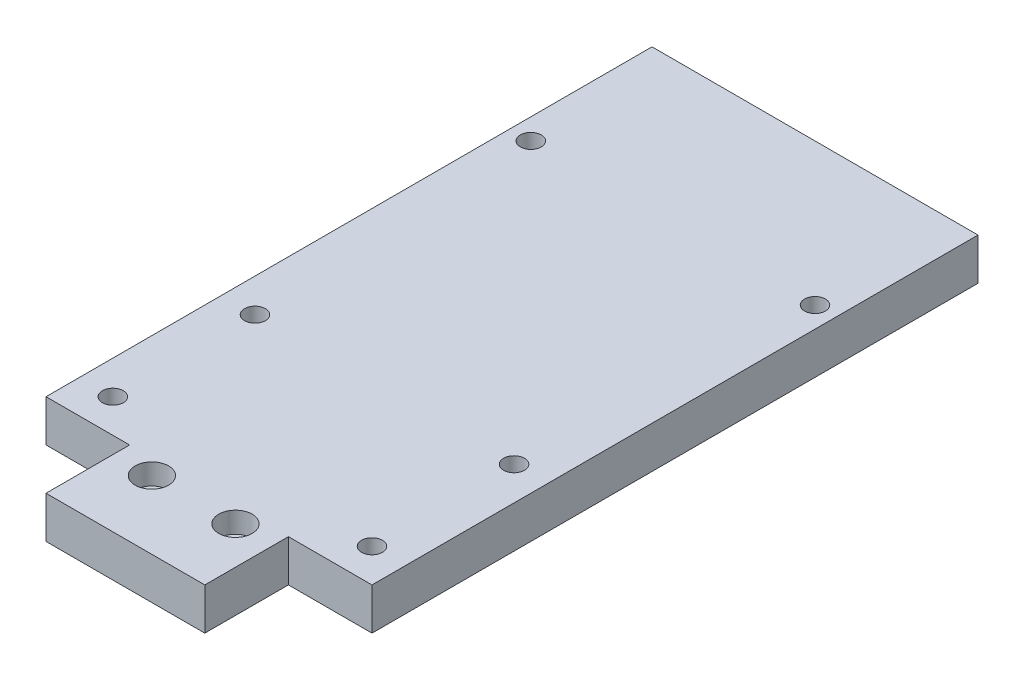
SolidWorks part; units mm, degrees
ref_plane "Front Plane" through (0, 0, 0) normal (0, 0, 1) x (1, 0, 0)
ref_plane "Top Plane" through (0, 0, 0) normal (0, 1, 0) x (1, 0, 0)
ref_plane "Right Plane" through (0, 0, 0) normal (1, 0, 0) x (0, 0, -1)
sketch "Sketch1" plane through (0, 0, 0) normal (0, 1, 0) x (1, 0, 0)
  line L0 (0, 0) -> (38, 0)
  line L1 (38, 0) -> (38, 20)
  line L2 (38, 20) -> (58, 20)
  line L3 (58, 20) -> (58, 165)
  line L4 (58, 165) -> (-20, 165)
  line L5 (-20, 165) -> (-20, 20)
  line L6 (-20, 20) -> (0, 20)
  line L7 (0, 20) -> (0, 0)
  dimension "D1" = 145
  dimension "D2" = 20
  dimension "D3" = 38
  dimension "D4" = 20
extrude "Boss-Extrude1" add sketch "Sketch1" along normal blind 10
sketch "Sketch2" plane through (0, 10, 0) normal (0, 1, 0) x (1, 0, 0)
  line L0 (0, 20) -> (0, 0) construction
  line L1 (38, 0) -> (38, 20) construction
  circle A0 centre (9, 16.3299) radius 4
  circle A1 centre (29, 16.3299) radius 4
  dimension "D1" = 8
  dimension "D2" = 9
  dimension "D3" = 9
extrude "Cut-Extrude1" cut sketch "Sketch2" against normal blind 5
sketch "Sketch3" plane through (0, 5, 0) normal (0, 1, 0) x (1, 0, 0)
  circle A0 centre (9, 16.3299) radius 2.5
  circle A1 centre (29, 16.3299) radius 2.5
  dimension "D1" = 5
extrude "Cut-Extrude2" cut sketch "Sketch3" against normal through all
sketch "Sketch5" plane through (0, 0, 0) normal (0, -1, 0) x (1, 0, 0)
  line L0 (-20, -165) -> (-20, -20) construction
  line L1 (58, -20) -> (58, -165) construction
  line L2 (58, -165) -> (-20, -165) construction
  line L3 (-20, -20) -> (0, -20) construction
  line L4 (38, -20) -> (58, -20) construction
  circle A0 centre (-15, -131) radius 4
  circle A1 centre (53, -131) radius 4
  circle A2 centre (-12, -28) radius 4
  circle A3 centre (50, -28) radius 4
  circle A4 centre (-12, -62) radius 4
  circle A5 centre (50, -62) radius 4
  point P12 (-15, -32.1055)
  point P15 (53, -32.1055)
  point P22 (-12, -51.3869)
  point P25 (50, -51.3869)
  dimension "D1" = 8
  dimension "D2" = 5
  dimension "D3" = 5
  dimension "D4" = 34
  dimension "D5" = 8
  dimension "D6" = 8
  dimension "D7" = 8
  dimension "D8" = 8
  dimension "D9" = 34
  dimension "D10" = 34
extrude "Cut-Extrude3" cut sketch "Sketch5" against normal blind 5
sketch "Sketch6" plane through (0, 5, 0) normal (0, -1, 0) x (1, 0, 0)
  circle A0 centre (-15, -131) radius 2.5
  circle A1 centre (53, -131) radius 2.5
  circle A2 centre (-12, -28) radius 2.5
  circle A3 centre (50, -28) radius 2.5
  circle A4 centre (-12, -62) radius 2.5
  circle A5 centre (50, -62) radius 2.5
  point P8 (-12, -28)
  point P12 (50, -28)
  point P16 (-12, -62)
  point P20 (50, -62)
  dimension "D1" = 5
extrude "Cut-Extrude4" cut sketch "Sketch6" against normal blind 5
